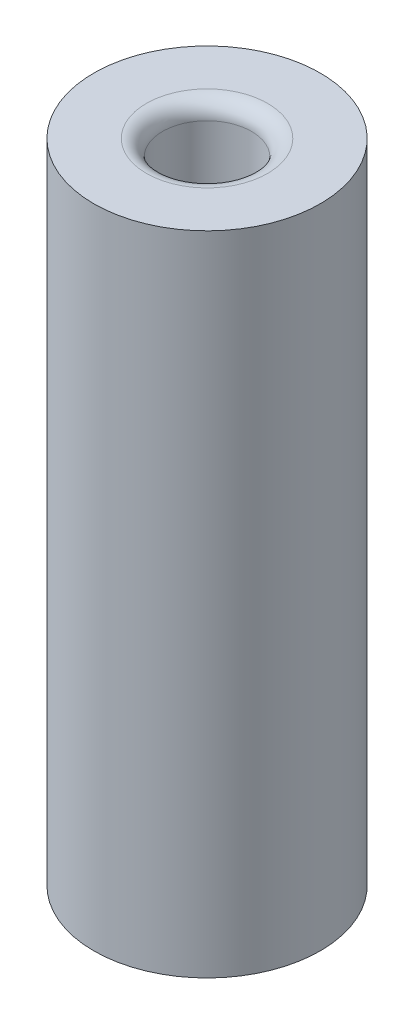
SolidWorks part; units mm, degrees
ref_plane "Front" through (0, 0, 0) normal (0, 0, 1) x (1, 0, 0)
ref_plane "Top" through (0, 0, 0) normal (0, 1, 0) x (1, 0, 0)
ref_plane "Right" through (0, 0, 0) normal (1, 0, 0) x (0, 0, -1)
sketch "Sketch1" plane through (0, 0, 0) normal (0, 1, 0) x (1, 0, 0)
  circle A0 centre (0, 0) radius 0.3556
  circle A1 centre (0, 0) radius 0.1397
  dimension "D1" = 0.7112
  dimension "D2" = 0.2794
extrude "Boss-Extrude1" add sketch "Sketch1" along normal blind 2.159
sketch "Sketch2" plane through (0, 2.159, 0) normal (0, 1, 0) x (1, 0, 0)
  circle A1 centre (0, 0) radius 0.4064
  dimension "D1" = 0.8128
extrude "Cut-Extrude1" cut sketch "Sketch2" against normal blind 0.127
fillet "Fillet1" radius 0.0508 1 edges at (0, 2.032, 0.1397)
